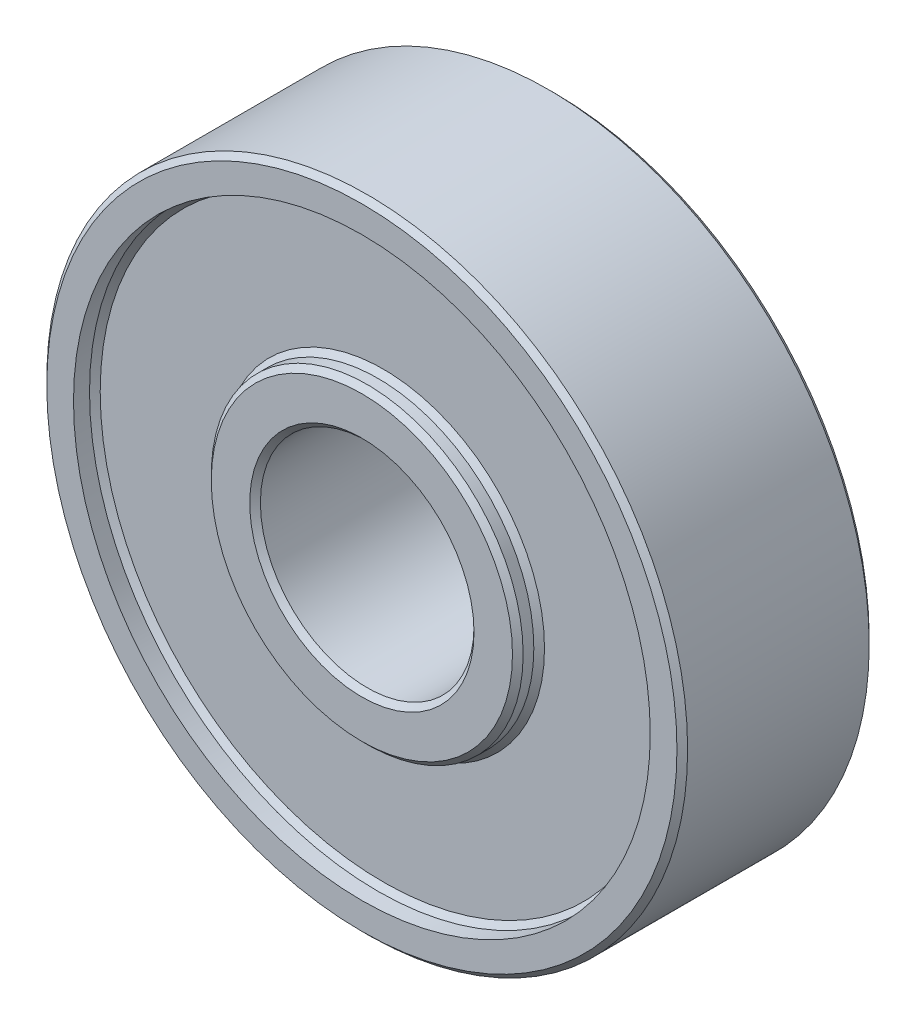
SolidWorks part; units mm, degrees
material "Литая легированная сталь"
ref_plane "Спереди" through (0, 0, 0) normal (0, 0, 1) x (1, 0, 0)
ref_plane "Сверху" through (0, 0, 0) normal (0, 1, 0) x (1, 0, 0)
ref_plane "Справа" through (0, 0, 0) normal (1, 0, 0) x (0, 0, -1)
sketch "Эскиз1" plane through (0, 0, 0) normal (0, 0, 1) x (1, 0, 0)
  circle A0 centre (0, 0) radius 15
extrude "Бобышка-Вытянуть1" add sketch "Эскиз1" along normal blind 9
sketch "Эскиз2" plane through (0, 0, 0) normal (0, 0, -1) x (-1, 0, 0)
  circle A0 centre (0, 0) radius 5
extrude "Вырез-Вытянуть1" cut sketch "Эскиз2" against normal through all
ref_axis "Ось1" through (0, 0, 9) along (0, 0, -1)
sketch "Эскиз3" plane through (0, 0, 0) normal (0, 1, 0) x (1, 0, 0)
  line L1 (15, 0) -> (-15, 0) construction
  line L2 (-15, -9) -> (15, -9) construction
  line L3 (7.3, -9) -> (13.5, -9)
  line L4 (7.3, -9) -> (7.3, -8)
  line L6 (7.3, 0) -> (13.5, 0)
  line L7 (7.3, 0) -> (7.3, -1)
  line L8 (7.3, -1) -> (13.5, -1)
  line L9 (13.5, 0) -> (13.5, -1)
  line L10 (7.3, -8) -> (13.5, -8)
  line L11 (13.5, -9) -> (13.5, -8)
  dimension "D1" = 7.3
  dimension "D2" = 13.5
  dimension "D3" = 1
revolve "Вырез-Повернуть1" cut sketch "Эскиз3" angle 360 about axis through (0, 0, 9) along (0, 0, -1)
chamfer "Фаска1" distance 0.25 angle 45 10 edges at (-5, 0, 0) (-5, 0, 9) (7.3, 0, 1) (13.5, 0, 1) (15, 0, 0) (15, 0, 9) (7.3, 0, 9) (7.3, 0, 0) (13.5, 0, 8) (7.3, 0, 8)
